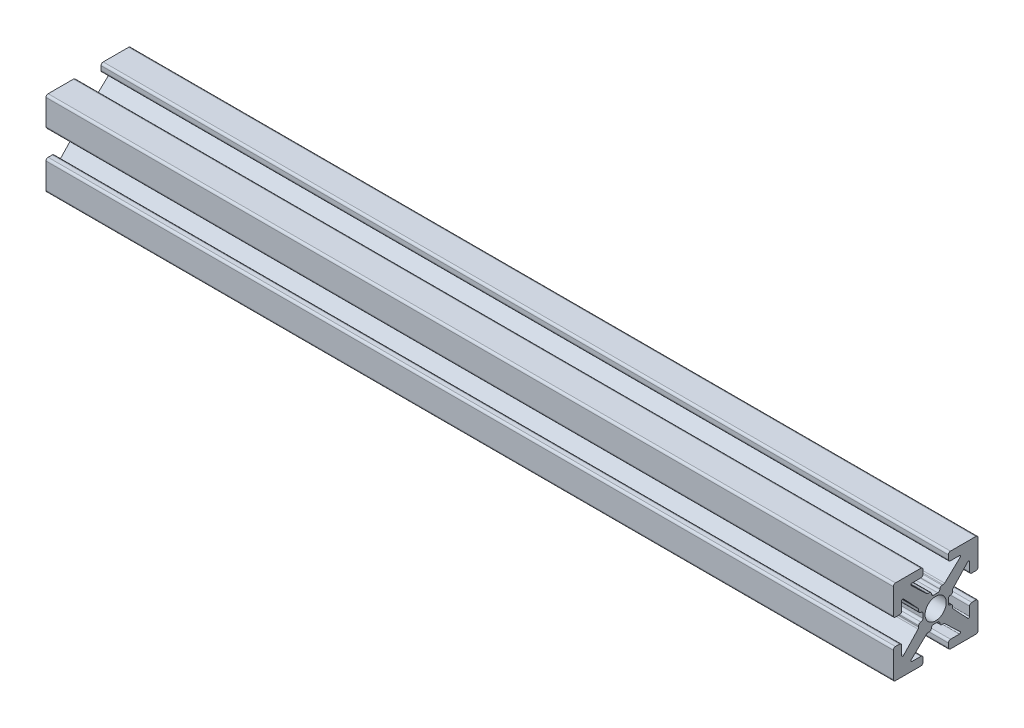
SolidWorks part; units mm, degrees
material "1060 Сплав"
ref_plane "Front Plane" through (0, 0, 0) normal (0, 0, 1) x (1, 0, 0)
ref_plane "Top Plane" through (0, 0, 0) normal (0, 1, 0) x (1, 0, 0)
ref_plane "Right Plane" through (0, 0, 0) normal (1, 0, 0) x (0, 0, -1)
sketch "Sketch1" plane through (0, 0, 0) normal (1, 0, 0) x (0, 0, -1)
  line L0 (0, 0) -> (0, 1.4948) construction
  line L1 (-0.2413, 1.4948) -> (0.2413, 1.4948)
  line L2 (5, 1.7526) -> (5, 4.746)
  line L3 (0.7493, 2.0028) -> (0.8899, 2.0028)
  line L4 (1.0639, 2.0718) -> (2.8908, 3.7899)
  line L5 (2.8038, 4.0094) -> (1.7526, 4.0094)
  line L6 (1.4986, 4.2634) -> (1.4986, 4.746)
  line L7 (1.7526, 5) -> (4.746, 5)
  line L8 (5, 5) -> (0, 0) construction
  line L9 (0, 0) -> (8.6271, 0) construction
  line L10 (0, 0) -> (0, 5) construction
  line L11 (4.2634, 1.4986) -> (4.746, 1.4986)
  line L12 (4.0094, 2.8038) -> (4.0094, 1.7526)
  line L13 (2.0718, 1.0639) -> (3.7899, 2.8908)
  line L14 (2.0028, 0.7493) -> (2.0028, 0.8899)
  line L15 (1.4948, -0.2413) -> (1.4948, 0.2413)
  line L16 (0, 0) -> (1.4948, 0) construction
  line L17 (-0.2413, -1.4948) -> (0.2413, -1.4948)
  line L18 (0.7493, -2.0028) -> (0.8899, -2.0028)
  line L19 (1.0639, -2.0718) -> (2.8908, -3.7899)
  line L20 (2.8038, -4.0094) -> (1.7526, -4.0094)
  line L21 (1.4986, -4.2634) -> (1.4986, -4.746)
  line L22 (1.7526, -5) -> (4.746, -5)
  line L23 (5, -1.7526) -> (5, -4.746)
  line L24 (4.2634, -1.4986) -> (4.746, -1.4986)
  line L25 (4.0094, -2.8038) -> (4.0094, -1.7526)
  line L26 (2.0718, -1.0639) -> (3.7899, -2.8908)
  line L27 (2.0028, -0.7493) -> (2.0028, -0.8899)
  line L28 (-0.7493, 2.0028) -> (-0.8899, 2.0028)
  line L29 (-1.0639, 2.0718) -> (-2.8908, 3.7899)
  line L30 (-2.8038, 4.0094) -> (-1.7526, 4.0094)
  line L31 (-1.4986, 4.2634) -> (-1.4986, 4.746)
  line L32 (-1.7526, 5) -> (-4.746, 5)
  line L33 (-5, 1.7526) -> (-5, 4.746)
  line L34 (-4.2634, 1.4986) -> (-4.746, 1.4986)
  line L35 (-4.0094, 2.8038) -> (-4.0094, 1.7526)
  line L36 (-2.0718, 1.0639) -> (-3.7899, 2.8908)
  line L37 (-2.0028, 0.7493) -> (-2.0028, 0.8899)
  line L38 (-1.4948, -0.2413) -> (-1.4948, 0.2413)
  line L39 (-2.0028, -0.7493) -> (-2.0028, -0.8899)
  line L40 (-2.0718, -1.0639) -> (-3.7899, -2.8908)
  line L41 (-4.0094, -2.8038) -> (-4.0094, -1.7526)
  line L42 (-4.2634, -1.4986) -> (-4.746, -1.4986)
  line L43 (-5, -1.7526) -> (-5, -4.746)
  line L44 (-1.7526, -5) -> (-4.746, -5)
  line L45 (-1.4986, -4.2634) -> (-1.4986, -4.746)
  line L46 (-2.8038, -4.0094) -> (-1.7526, -4.0094)
  line L47 (-1.0639, -2.0718) -> (-2.8908, -3.7899)
  line L48 (-0.7493, -2.0028) -> (-0.8899, -2.0028)
  arc A0 (2.8908, 3.7899) -> (2.8038, 4.0094) centre (2.8038, 3.8824) ccw
  arc A1 (0.4953, 1.7488) -> (0.7493, 2.0028) centre (0.7493, 1.7488) cw
  arc A2 (0.8899, 2.0028) -> (1.0639, 2.0718) centre (0.8899, 2.2568) ccw
  arc A3 (1.7526, 4.0094) -> (1.4986, 4.2634) centre (1.7526, 4.2634) cw
  arc A4 (1.4986, 4.746) -> (1.7526, 5) centre (1.7526, 4.746) cw
  arc A5 (0.2413, 1.4948) -> (0.4953, 1.7488) centre (0.2413, 1.7488) ccw
  arc A6 (4.746, 1.4986) -> (5, 1.7526) centre (4.746, 1.7526) ccw
  arc A7 (4.0094, 1.7526) -> (4.2634, 1.4986) centre (4.2634, 1.7526) ccw
  arc A8 (3.7899, 2.8908) -> (4.0094, 2.8038) centre (3.8824, 2.8038) cw
  arc A9 (2.0028, 0.8899) -> (2.0718, 1.0639) centre (2.2568, 0.8899) cw
  arc A10 (1.7488, 0.4953) -> (2.0028, 0.7493) centre (1.7488, 0.7493) ccw
  arc A11 (1.4948, 0.2413) -> (1.7488, 0.4953) centre (1.7488, 0.2413) cw
  arc A12 (0.2413, -1.4948) -> (0.4953, -1.7488) centre (0.2413, -1.7488) cw
  arc A13 (0.4953, -1.7488) -> (0.7493, -2.0028) centre (0.7493, -1.7488) ccw
  arc A14 (0.8899, -2.0028) -> (1.0639, -2.0718) centre (0.8899, -2.2568) cw
  arc A15 (2.8908, -3.7899) -> (2.8038, -4.0094) centre (2.8038, -3.8824) cw
  arc A16 (1.7526, -4.0094) -> (1.4986, -4.2634) centre (1.7526, -4.2634) ccw
  arc A17 (1.4986, -4.746) -> (1.7526, -5) centre (1.7526, -4.746) ccw
  arc A18 (4.746, -1.4986) -> (5, -1.7526) centre (4.746, -1.7526) cw
  arc A19 (4.0094, -1.7526) -> (4.2634, -1.4986) centre (4.2634, -1.7526) cw
  arc A20 (3.7899, -2.8908) -> (4.0094, -2.8038) centre (3.8824, -2.8038) ccw
  arc A21 (2.0028, -0.8899) -> (2.0718, -1.0639) centre (2.2568, -0.8899) ccw
  arc A22 (1.7488, -0.4953) -> (2.0028, -0.7493) centre (1.7488, -0.7493) cw
  arc A23 (1.4948, -0.2413) -> (1.7488, -0.4953) centre (1.7488, -0.2413) ccw
  arc A24 (-0.2413, 1.4948) -> (-0.4953, 1.7488) centre (-0.2413, 1.7488) cw
  arc A25 (-0.4953, 1.7488) -> (-0.7493, 2.0028) centre (-0.7493, 1.7488) ccw
  arc A26 (-0.8899, 2.0028) -> (-1.0639, 2.0718) centre (-0.8899, 2.2568) cw
  arc A27 (-2.8908, 3.7899) -> (-2.8038, 4.0094) centre (-2.8038, 3.8824) cw
  arc A28 (-1.7526, 4.0094) -> (-1.4986, 4.2634) centre (-1.7526, 4.2634) ccw
  arc A29 (-1.4986, 4.746) -> (-1.7526, 5) centre (-1.7526, 4.746) ccw
  arc A30 (-4.746, 1.4986) -> (-5, 1.7526) centre (-4.746, 1.7526) cw
  arc A31 (-4.0094, 1.7526) -> (-4.2634, 1.4986) centre (-4.2634, 1.7526) cw
  arc A32 (-3.7899, 2.8908) -> (-4.0094, 2.8038) centre (-3.8824, 2.8038) ccw
  arc A33 (-2.0028, 0.8899) -> (-2.0718, 1.0639) centre (-2.2568, 0.8899) ccw
  arc A34 (-1.7488, 0.4953) -> (-2.0028, 0.7493) centre (-1.7488, 0.7493) cw
  arc A35 (-1.4948, 0.2413) -> (-1.7488, 0.4953) centre (-1.7488, 0.2413) ccw
  arc A36 (-1.4948, -0.2413) -> (-1.7488, -0.4953) centre (-1.7488, -0.2413) cw
  arc A37 (-1.7488, -0.4953) -> (-2.0028, -0.7493) centre (-1.7488, -0.7493) ccw
  arc A38 (-2.0028, -0.8899) -> (-2.0718, -1.0639) centre (-2.2568, -0.8899) cw
  arc A39 (-3.7899, -2.8908) -> (-4.0094, -2.8038) centre (-3.8824, -2.8038) cw
  arc A40 (-4.0094, -1.7526) -> (-4.2634, -1.4986) centre (-4.2634, -1.7526) ccw
  arc A41 (-4.746, -1.4986) -> (-5, -1.7526) centre (-4.746, -1.7526) ccw
  arc A42 (-1.4986, -4.746) -> (-1.7526, -5) centre (-1.7526, -4.746) cw
  arc A43 (-1.7526, -4.0094) -> (-1.4986, -4.2634) centre (-1.7526, -4.2634) cw
  arc A44 (-2.8908, -3.7899) -> (-2.8038, -4.0094) centre (-2.8038, -3.8824) ccw
  arc A45 (-0.8899, -2.0028) -> (-1.0639, -2.0718) centre (-0.8899, -2.2568) ccw
  arc A46 (-0.4953, -1.7488) -> (-0.7493, -2.0028) centre (-0.7493, -1.7488) cw
  arc A47 (-0.2413, -1.4948) -> (-0.4953, -1.7488) centre (-0.2413, -1.7488) ccw
  arc A48 (-4.746, 5) -> (-5, 4.746) centre (-4.746, 4.746) ccw
  arc A49 (-5, -4.746) -> (-4.746, -5) centre (-4.746, -4.746) ccw
  arc A50 (4.746, -5) -> (5, -4.746) centre (4.746, -4.746) ccw
  arc A51 (4.746, 5) -> (5, 4.746) centre (4.746, 4.746) cw
  point P14 (3.1242, 4.0094)
  point P19 (0.9906, 2.0028)
  point P150 (0, -1.4948)
  point P152 (-5, 5)
  point P155 (-5, -5)
  point P158 (5, -5)
  dimension "D10" = 0.127
  dimension "D11" = 0.254
  dimension "D2" = 0.254
  dimension "D1" = 10
  dimension "D3" = 2.9972
  dimension "D4" = 0.508
  dimension "D5" = 2.9972
  dimension "D6" = 0.9906
  dimension "D7" = 1.6256
  dimension "D8" = 1.9812
  dimension "D9" = 0.9906
extrude "Estrusione-Estrusione1" add sketch "Sketch1" along normal blind 100 contours L36 A32 L35 A31 L34 A30 L33 A48 L32 A29 L31 A28 L30 A27 L29 A26 L28 A25 A24 L1 A5 A1 L3 A2 L4 A0 L5 A3 L6 A4 L7 A51 L2 A6 L11 A7 L12 A8 L13 A9 L14 A10 A11 L15 A23 A22 L27 A21 L26 A20 L25 A19 L24 A18 L23 A50 L22 A17 L21 A16 L20 A15 L19 A14 L18 A13 A12 L17 A47 A46 L48 A45 L47 A44 L46 A43 L45 A42 L44 A49 L43 A41 L42 A40 L41 A39 L40 A38 L39 A37 A36 L38 A35 A34 L37 A33
hole_wizard "Foro filettato M3x0.5-1" positions "Schizzo2" profile "Schizzo1" tap size "M3x0.5" standard "Ansi Metric" end condition through all
sketch "Schizzo2" plane through (0, 0, 0) normal (-1, 0, 0) x (0, 0, 1)
  point P0 (0, 0)
sketch "Schizzo1" plane through (0, 0, 0) normal (0, 1, 0) x (0, 0, 1)
  line L0 (0, 0) -> (0, 100)
  line L1 (0, 100) -> (1.25, 100)
  line L2 (1.25, 100) -> (1.25, 0)
  line L5 (1.25, 0) -> (0, 0)
  line L11 (0, -6.35) -> (0, 107.95) construction
  dimension "Thread Major Dia." = 2.5
  dimension "Thru Tap Drill Depth" = 100
equation "\"camera plate width\"=220"
equation "\"camera plate length\"=220"
equation "\"camera height\"= 100"
equation "\"D1@Estrusione-Estrusione1\"=\"zero height\""
equation "\"zero height\"= 100"
